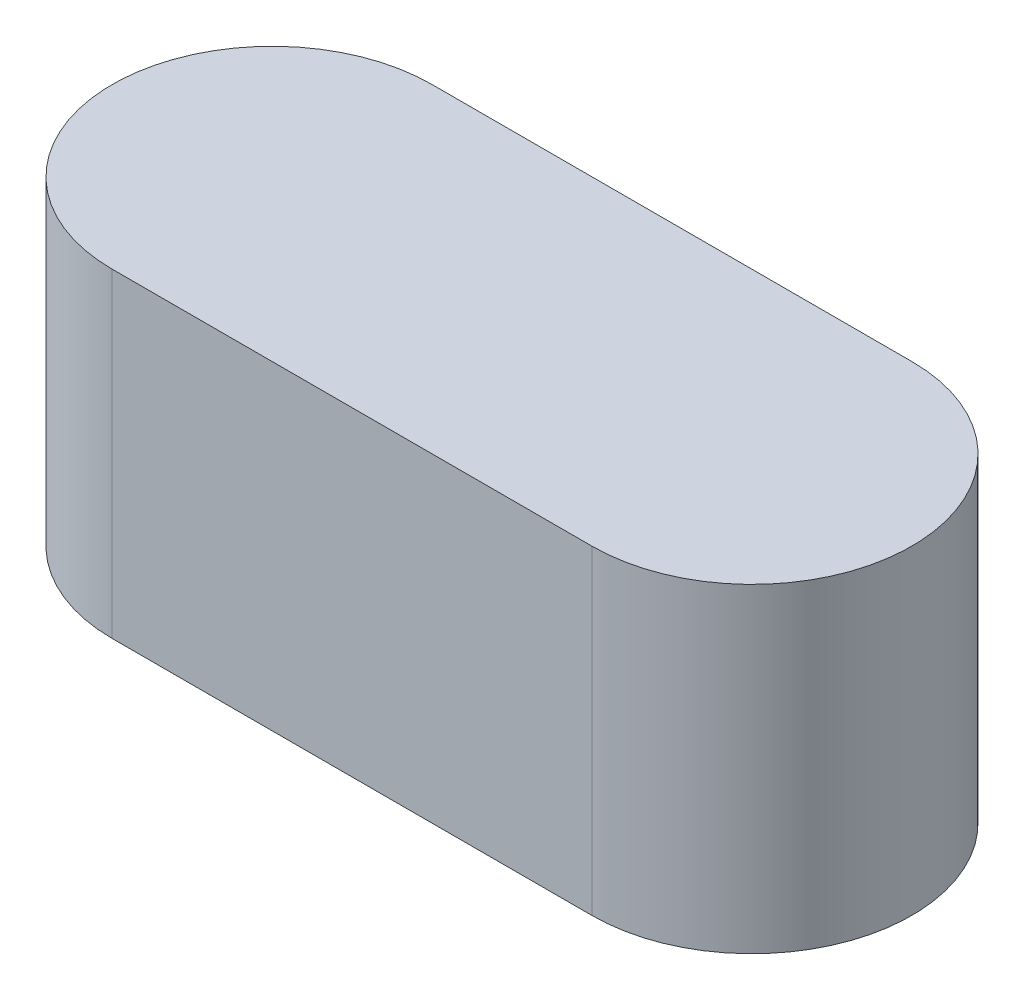
SolidWorks part; units mm, degrees
ref_plane "前视基准面" through (0, 0, 0) normal (0, 0, 1) x (1, 0, 0)
ref_plane "上视基准面" through (0, 0, 0) normal (0, 1, 0) x (1, 0, 0)
ref_plane "右视基准面" through (0, 0, 0) normal (1, 0, 0) x (0, 0, -1)
sketch "草图1" plane through (0, 0, 0) normal (0, 1, 0) x (1, 0, 0)
  circle A0 centre (0, 0) radius 10
extrude "凸台-拉伸1" add sketch "草图1" along normal blind 20
sketch "草图2" plane through (0, 20, 0) normal (0, 1, 0) x (1, 0, 0)
  line L1 (0, 10) -> (30, 10)
  line L2 (0, 10) -> (0, -10)
  line L3 (0, -10) -> (30, -10)
  circle A0 centre (0, 0) radius 10 construction
  arc A1 (30, -10) -> (30, 10) centre (30, 0) ccw
  dimension "D1" = 30
extrude "凸台-拉伸2" add sketch "草图2" against normal blind 20
